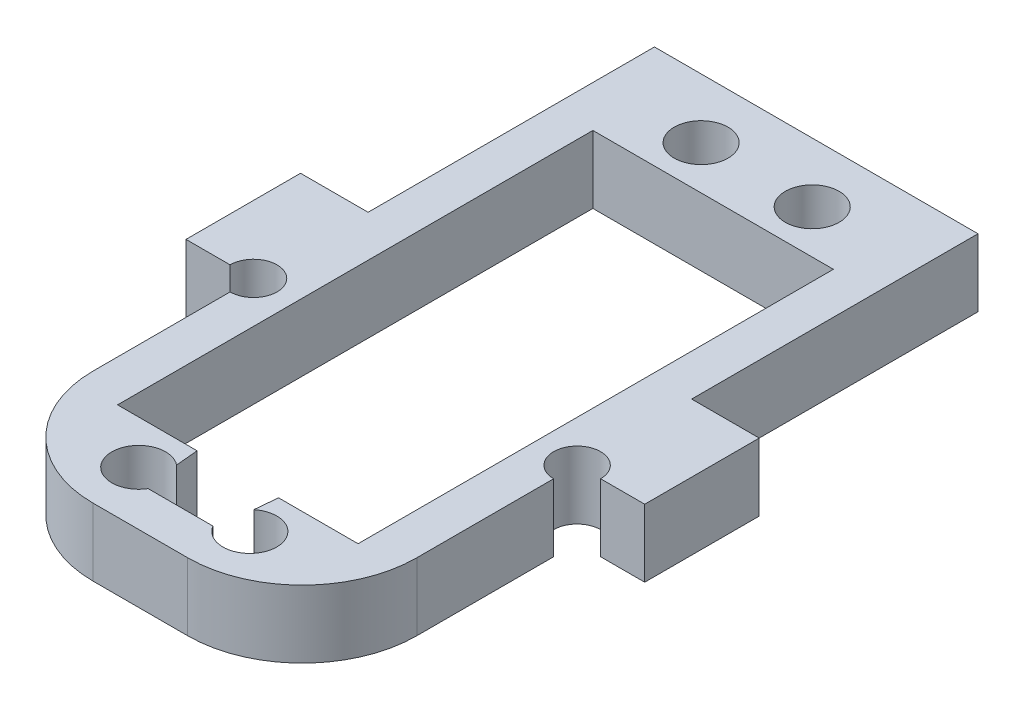
SolidWorks part; units mm, degrees
ref_plane "Front Plane" through (0, 0, 0) normal (0, 0, 1) x (1, 0, 0)
ref_plane "Top Plane" through (0, 0, 0) normal (0, 1, 0) x (1, 0, 0)
ref_plane "Right Plane" through (0, 0, 0) normal (1, 0, 0) x (0, 0, -1)
sketch "Sketch1" plane through (0, 0, 0) normal (0, 1, 0) x (1, 0, 0)
  line L1 (-14.125, -28) -> (14.125, -28)
  line L2 (-14.125, -28) -> (-14.125, 30)
  line L3 (-14.125, 30) -> (14.125, 30)
  line L4 (14.125, -28) -> (14.125, 30)
  line L5 (-14.125, -28) -> (14.125, 30) construction
  line L6 (-14.125, 30) -> (14.125, -28) construction
  point P0 (0, 1)
  dimension "D1" = 28.25
  dimension "D2" = 28
  dimension "D3" = 30
extrude "Boss-Extrude1" add sketch "Sketch1" along normal blind 5.9
sketch "Sketch2" plane through (0, 5.9, 0) normal (0, 1, 0) x (1, 0, 0)
  line L0 (-14.125, -28) -> (14.125, -28) construction
  line L1 (-10, 20.5) -> (10, 20.5)
  line L2 (-10, 20.5) -> (-10, -20)
  line L3 (-10, -20) -> (10, -20)
  line L4 (10, 20.5) -> (10, -20)
  line L5 (-10, 20.5) -> (10, -20) construction
  line L6 (-10, -20) -> (10, 20.5) construction
  line L7 (-14.125, 30) -> (-14.125, -28) construction
  line L22 (0, -28) -> (0, 30) construction
  line L23 (14.125, 30) -> (-14.125, 30) construction
  line L24 (0, -24.3) -> (-4.85, -24.3) construction
  line L25 (0, 0.25) -> (-10, 0.25) construction
  circle A4 centre (-4.85, -24.3) radius 2.35
  circle A5 centre (-4.85, 24.8) radius 2.35
  circle A6 centre (4.85, 24.8) radius 2.35
  circle A7 centre (4.85, -24.3) radius 2.35
  point P0 (0, 0.25)
  point P9 (-14.125, 1)
  dimension "D9" = 4.7
  dimension "D1" = 40.5
  dimension "D2" = 20
  dimension "D3" = 24.3
  dimension "D10" = 4.85
  dimension "D11" = 4.3
extrude "Cut-Extrude1" cut sketch "Sketch2" against normal up to next
sketch "Sketch3" plane through (0, 5.9, 0) normal (0, 1, 0) x (1, 0, 0)
  line L0 (-14.125, 5) -> (-20.025, 5)
  line L1 (-14.125, 5) -> (-14.125, -5)
  line L2 (-14.125, -5) -> (-20.025, -5)
  line L3 (-20.025, 5) -> (-20.025, -5)
  line L4 (0, 30.9283) -> (0, 24.4049) construction
  line L5 (14.125, -5) -> (20.025, -5)
  line L6 (20.025, 5) -> (20.025, -5)
  line L7 (14.125, 5) -> (20.025, 5)
  line L8 (14.125, 5) -> (14.125, -5)
  line L9 (-14.125, 30) -> (-14.125, -28) construction
  point P10 (-20.025, 0)
  dimension "D2" = 10
  dimension "D3" = 5.9
extrude "Boss-Extrude2" add sketch "Sketch3" against normal up to surface (5.9 mm away) up to face at (4.85, 0, 21.95)
sketch "Sketch4" plane through (0, 5.9, 0) normal (0, 1, 0) x (1, 0, 0)
  circle A0 centre (-14.125, -5) radius 2.05
  circle A1 centre (14.125, -5) radius 2.05
  dimension "D1" = 4.1
extrude "Cut-Extrude2" cut sketch "Sketch4" against normal up to next
sketch "Sketch5" plane through (0, 5.9, 0) normal (0, 1, 0) x (1, 0, 0)
  line L0 (3.1, -20) -> (3.6, -20)
  line L1 (-10, -20) -> (10, -20) construction
  line L2 (3.6, -20) -> (3.1, -25.5)
  line L4 (3.1, -25.5) -> (3.1, -20) construction
  line L5 (3.1, -20) -> (0, -20)
  line L6 (0, -20) -> (0, -25.5) construction
  line L7 (-3.1, -25.5) -> (3.1, -25.5)
  line L8 (-3.6, -20) -> (-3.1, -25.5)
  line L9 (-3.1, -20) -> (-3.6, -20)
  line L10 (-3.1, -20) -> (0, -20)
  dimension "D1" = 5.5
  dimension "D2" = 0.5
  dimension "D3" = 3.1
extrude "Cut-Extrude3" cut sketch "Sketch5" against normal blind 10
sketch "Sketch6" plane through (0, 0, 28) normal (0, 0, 1) x (1, 0, 0)
  line L4 (-14.125, 0) -> (14.125, 0)
  line L5 (14.125, 0) -> (14.125, 5.9)
  line L6 (14.125, 5.9) -> (-14.125, 5.9)
  line L7 (-14.125, 5.9) -> (-14.125, 0)
  line L8 (-14.125, 0) -> (14.125, 0)
  line L9 (14.125, 0) -> (14.125, 5.9)
  line L10 (14.125, 5.9) -> (-14.125, 5.9)
  line L11 (-14.125, 5.9) -> (-14.125, 0)
  dimension "D1" = 0
extrude "Boss-Extrude3" add sketch "Sketch6" along normal blind 1
fillet "Fillet1" radius 10 2 edges at (14.125, 2.95, 29) (-14.125, 2.95, 29)
sketch "Sketch7" plane through (0, 5.9, 0) normal (0, 1, 0) x (1, 0, 0)
  line L0 (-10, 20.5) -> (-10, -20) construction
  line L1 (-10.5, -20.5) -> (10.5, -20.5)
  line L2 (-10.5, -20.5) -> (-10.5, 21)
  line L3 (-10.5, 21) -> (10.5, 21)
  line L4 (10.5, -20.5) -> (10.5, 21)
  line L5 (-10.5, -20.5) -> (10.5, 21) construction
  line L6 (-10.5, 21) -> (10.5, -20.5) construction
  line L7 (10, 20.5) -> (-10, 20.5) construction
  line L8 (10, -20) -> (10, 20.5) construction
  point P0 (0, 0.25)
  point P7 (-10, 0.25)
  point P10 (0, 20.5)
  dimension "D1" = 0.5
  dimension "D2" = 0.5
extrude "Cut-Extrude4" cut sketch "Sketch7" against normal up to next
equation "\"e\" = 5.9"
equation "\"D1@Boss-Extrude1\"=\"e\""
equation "\"D3@Sketch3\"= \"e\""
